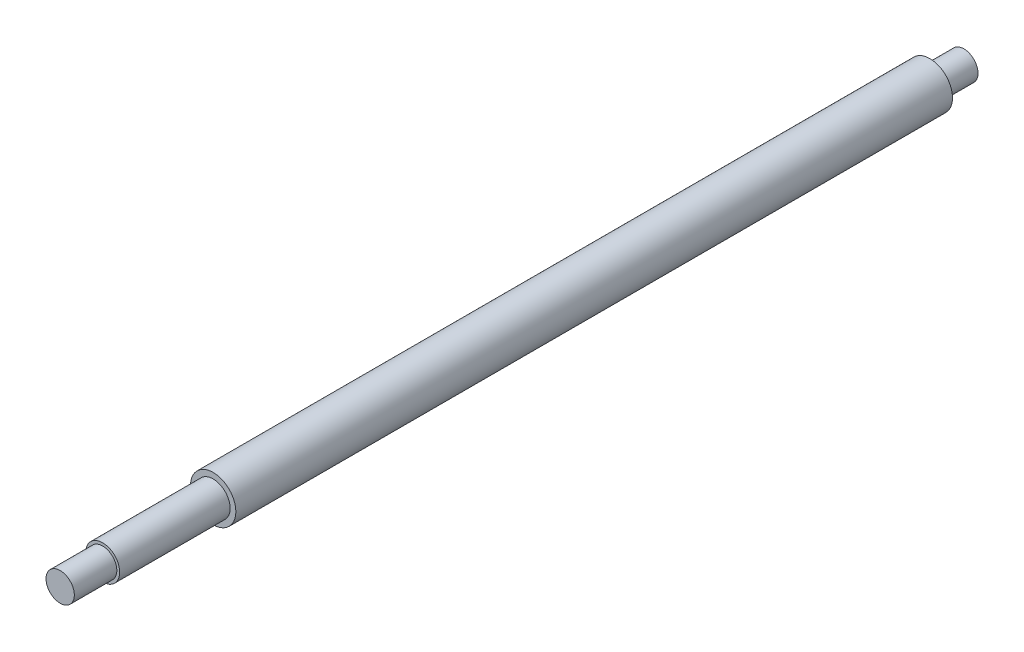
SolidWorks part; units mm, degrees
material "1060 Alloy"
ref_plane "Front Plane" through (0, 0, 0) normal (0, 0, 1) x (1, 0, 0)
ref_plane "Top Plane" through (0, 0, 0) normal (0, 1, 0) x (1, 0, 0)
ref_plane "Right Plane" through (0, 0, 0) normal (1, 0, 0) x (0, 0, -1)
sketch "Sketch1" plane through (0, 0, 0) normal (1, 0, 0) x (0, 0, -1)
  line L0 (0, 0) -> (-42.623, 0) construction
  line L1 (-318.98, 0) -> (-318.98, 5)
  line L2 (-318.98, 5) -> (-303.98, 5)
  line L3 (-303.98, 5) -> (-303.98, 6)
  line L4 (-303.98, 6) -> (-264.98, 6)
  line L5 (-264.98, 6) -> (-264.98, 8)
  line L6 (-264.98, 8) -> (-12, 8)
  line L7 (-12, 8) -> (-12, 5)
  line L8 (-12, 5) -> (0, 5)
  line L9 (0, 5) -> (0, 0)
  line L10 (-318.98, 0) -> (0, 0)
  dimension "D1" = 5
  dimension "D2" = 6
  dimension "D3" = 8
  dimension "D4" = 5
  dimension "D5" = 12
  dimension "D6" = 39
  dimension "D7" = 15
  dimension "D8" = 252.98
revolve "Revolve1" add sketch "Sketch1" angle 360 about L0
sketch "Sketch3" [suppressed] plane through (0, 0, 0) normal (1, 0, 0) x (0, 0, -1)
  line L0 (-80.9254, 0) -> (-123.5483, 0) construction
  line L1 (-275.75, 0) -> (-275.75, 5)
  line L2 (-275.75, 5) -> (-260.75, 5)
  line L3 (-260.75, 5) -> (-260.75, 6)
  line L4 (-260.75, 6) -> (-221.75, 6)
  line L5 (-221.75, 6) -> (-221.75, 8)
  line L6 (-221.75, 8) -> (-12, 8)
  line L7 (-12, 8) -> (-12, 5)
  line L8 (-12, 5) -> (0, 5)
  line L9 (0, 5) -> (0, 0)
  line L10 (-275.75, 0) -> (0, 0)
  dimension "D1" = 10
  dimension "D2" = 6
  dimension "D3" = 8
  dimension "D4" = 10
  dimension "D5" = 15
  dimension "D6" = 39
  dimension "D7" = 209.75
  dimension "D8" = 12
revolve "Revolve2" [suppressed] add sketch "Sketch3" angle 360 about L0
